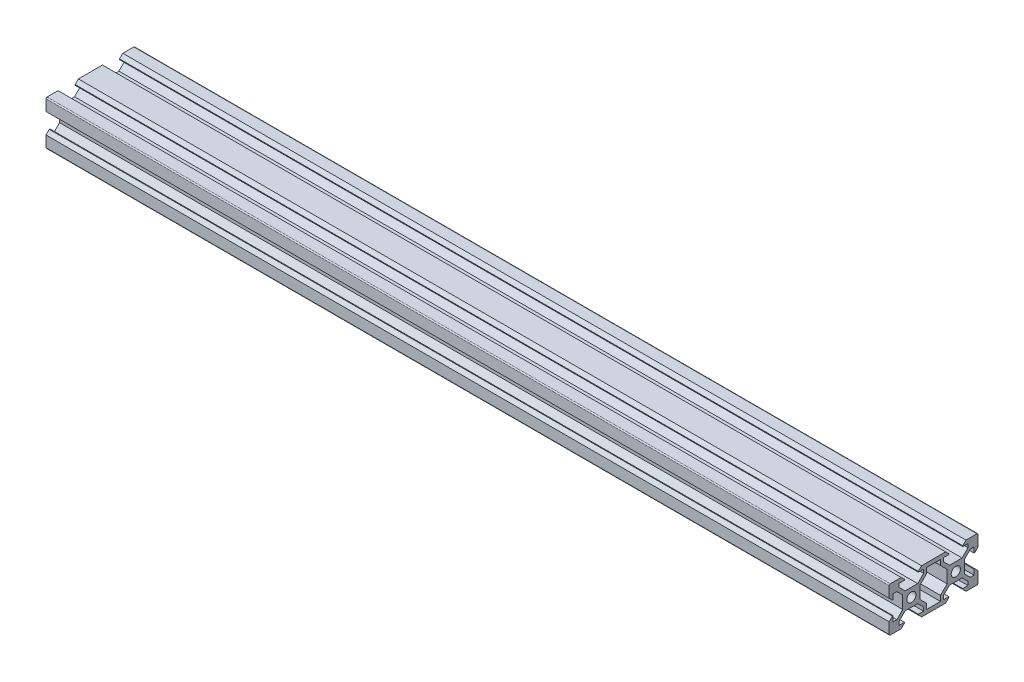
SolidWorks part; units mm, degrees
material "6063-T5"
ref_plane "Front Plane" through (0, 0, 0) normal (0, 0, 1) x (1, 0, 0)
ref_plane "Top Plane" through (0, 0, 0) normal (0, 1, 0) x (1, 0, 0)
ref_plane "Right Plane" through (0, 0, 0) normal (1, 0, 0) x (0, 0, -1)
sketch "Sketch2" plane through (0, 0, 0) normal (1, 0, 0) x (0, 0, -1)
  line L0 (3.1254, 8.5482) -> (3.1254, 8.2032)
  line L2 (-10.0054, 4.5832) -> (-10.0054, 9.5032)
  line L3 (-8.2054, 3.1232) -> (-8.5399, 3.1232)
  line L5 (3.8981, 2.8404) -> (3.8981, -2.8404)
  line L6 (-8.5399, 3.1232) -> (-10.0054, 4.5832)
  line L7 (-8.2054, 5.5032) -> (-8.2054, 3.1232)
  line L9 (-8.5399, -3.1232) -> (-10.0054, -4.5832)
  line L10 (-3.8981, 2.8404) -> (-6.5639, 5.4954)
  line L11 (-2.8396, 3.9032) -> (-5.5054, 6.5582)
  line L12 (-3.1254, 8.5482) -> (-3.1254, 8.2032)
  line L13 (-4.5804, 10.0032) -> (-9.5054, 10.0032)
  line L14 (-3.1254, 8.5482) -> (-4.5804, 10.0032)
  line L15 (5.5054, -6.5582) -> (2.8396, -3.9032)
  line L18 (5.5054, 8.2032) -> (5.5054, 6.5582)
  line L19 (5.5054, 8.2032) -> (3.1254, 8.2032)
  line L20 (3.1254, 8.5482) -> (4.5804, 10.0032)
  line L24 (2.8396, 3.9032) -> (5.5054, 6.5582)
  line L27 (-3.1254, -8.5482) -> (-4.5804, -10.0032)
  line L28 (-5.5054, -8.2032) -> (-3.1254, -8.2032)
  line L29 (-5.5054, -6.5582) -> (-5.5054, -8.2032)
  line L30 (-2.8396, -3.9032) -> (-5.5054, -6.5582)
  line L31 (-3.8981, -2.8404) -> (-6.5639, -5.4954)
  line L32 (-8.2054, -5.5032) -> (-8.2054, -3.1232)
  line L33 (-2.8396, 3.9032) -> (2.8396, 3.9032)
  line L34 (-10.0054, -4.5832) -> (-10.0054, -9.5032)
  line L35 (-5.5054, 6.5582) -> (-5.5054, 8.2032)
  line L36 (-5.5054, 8.2032) -> (-3.1254, 8.2032)
  line L37 (-8.2054, 5.5032) -> (-6.5639, 5.4954)
  line L39 (-6.5639, -5.4954) -> (-8.2054, -5.5032)
  line L40 (-3.1254, -8.2032) -> (-3.1254, -8.5482)
  line L41 (-9.5054, -10.0032) -> (-4.5804, -10.0032)
  line L42 (-8.2054, -3.1232) -> (-8.5399, -3.1232)
  line L46 (5.5054, -6.5582) -> (5.5054, -8.2032)
  line L47 (5.5054, -8.2032) -> (3.1254, -8.2032)
  line L48 (3.1254, -8.2032) -> (3.1254, -8.5482)
  line L49 (3.1254, -8.5482) -> (4.5804, -10.0032)
  line L50 (-3.8981, -2.8404) -> (-3.8981, 2.8404)
  line L51 (-2.8396, -3.9032) -> (2.8396, -3.9032)
  line L52 (22.8504, -3.9032) -> (17.1713, -3.9032)
  line L53 (23.9089, -2.8404) -> (23.9089, 2.8404)
  line L54 (16.8854, -8.5482) -> (15.4304, -10.0032)
  line L55 (16.8854, -8.2032) -> (16.8854, -8.5482)
  line L56 (14.5054, -8.2032) -> (16.8854, -8.2032)
  line L57 (14.5054, -6.5582) -> (14.5054, -8.2032)
  line L61 (28.2163, -3.1232) -> (28.5507, -3.1232)
  line L62 (29.5163, -10.0032) -> (24.5913, -10.0032)
  line L63 (23.1363, -8.2032) -> (23.1363, -8.5482)
  line L64 (26.5748, -5.4954) -> (28.2163, -5.5032)
  line L65 (28.2163, 5.5032) -> (26.5748, 5.4954)
  line L66 (25.5163, 8.2032) -> (23.1363, 8.2032)
  line L67 (25.5163, 6.5582) -> (25.5163, 8.2032)
  line L68 (30.0163, -4.5832) -> (30.0163, -9.5032)
  line L69 (22.8504, 3.9032) -> (17.1713, 3.9032)
  line L70 (28.2163, -5.5032) -> (28.2163, -3.1232)
  line L71 (23.9089, -2.8404) -> (26.5748, -5.4954)
  line L72 (22.8504, -3.9032) -> (25.5163, -6.5582)
  line L73 (25.5163, -6.5582) -> (25.5163, -8.2032)
  line L74 (25.5163, -8.2032) -> (23.1363, -8.2032)
  line L75 (23.1363, -8.5482) -> (24.5913, -10.0032)
  line L78 (17.1713, 3.9032) -> (14.5054, 6.5582)
  line L82 (16.8854, 8.5482) -> (15.4304, 10.0032)
  line L83 (14.5054, 8.2032) -> (16.8854, 8.2032)
  line L84 (14.5054, 8.2032) -> (14.5054, 6.5582)
  line L87 (14.5054, -6.5582) -> (17.1713, -3.9032)
  line L88 (23.1363, 8.5482) -> (24.5913, 10.0032)
  line L89 (24.5913, 10.0032) -> (29.5163, 10.0032)
  line L90 (23.1363, 8.5482) -> (23.1363, 8.2032)
  line L91 (22.8504, 3.9032) -> (25.5163, 6.5582)
  line L92 (23.9089, 2.8404) -> (26.5748, 5.4954)
  line L93 (28.5507, -3.1232) -> (30.0163, -4.5832)
  line L95 (28.2163, 5.5032) -> (28.2163, 3.1232)
  line L96 (28.5507, 3.1232) -> (30.0163, 4.5832)
  line L97 (16.1128, 2.8404) -> (16.1128, -2.8404)
  line L98 (28.2163, 3.1232) -> (28.5507, 3.1232)
  line L99 (30.0163, 4.5832) -> (30.0163, 9.5032)
  line L101 (16.8854, 8.5482) -> (16.8854, 8.2032)
  line L102 (4.5804, -10.0032) -> (15.4304, -10.0032)
  line L103 (4.5804, 10.0032) -> (15.4304, 10.0032)
  line L104 (6.9013, 8.2032) -> (13.1095, 8.2032)
  line L105 (3.8981, 2.8404) -> (6.9013, 5.8314)
  line L106 (13.1095, 8.2032) -> (13.1095, 5.8314)
  line L107 (6.9013, 8.2032) -> (6.9013, 5.8314)
  line L108 (16.1128, 2.8404) -> (13.1095, 5.8314)
  line L110 (13.1095, -8.2032) -> (13.1095, -5.8314)
  line L111 (16.1128, -2.8404) -> (13.1095, -5.8314)
  line L112 (3.8981, -2.8404) -> (6.9013, -5.8314)
  line L113 (6.9013, -8.2032) -> (6.9013, -5.8314)
  line L114 (6.9013, -8.2032) -> (13.1095, -8.2032)
  arc A0 (-9.5054, 10.0032) -> (-10.0054, 9.5032) centre (-9.5054, 9.5032) ccw
  arc A2 (-9.5054, -10.0032) -> (-10.0054, -9.5032) centre (-9.5054, -9.5032) cw
  circle A4 centre (0.0037, 0) radius 2.075
  circle A5 centre (20.0072, 0) radius 2.075
  arc A7 (29.5163, -10.0032) -> (30.0163, -9.5032) centre (29.5163, -9.5032) ccw
  arc A9 (29.5163, 10.0032) -> (30.0163, 9.5032) centre (29.5163, 9.5032) cw
  point P20 (10.0054, 8.2032)
  point P21 (10.0054, 10.0032)
  dimension "D1" = 1.8
  dimension "D2" = 6.2082
  dimension "D3" = 0
extrude "Boss-Extrude1" add sketch "Sketch2" along normal blind 380
